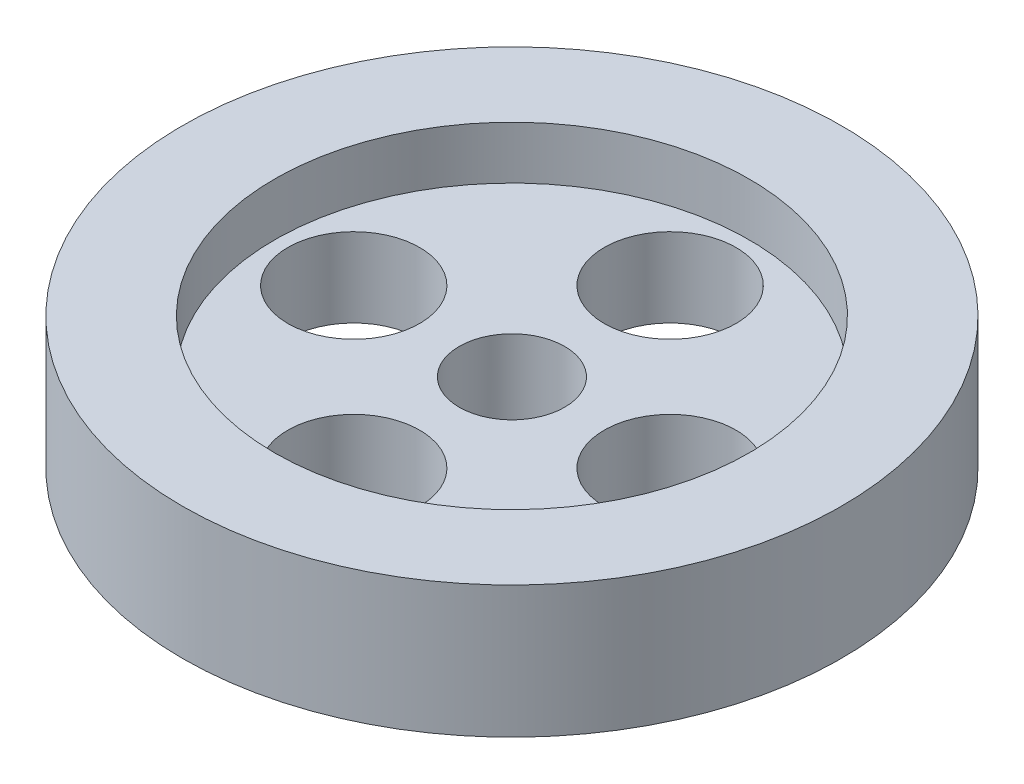
SolidWorks part; units mm, degrees
ref_plane "Front Plane" through (0, 0, 0) normal (0, 0, 1) x (1, 0, 0)
ref_plane "Top Plane" through (0, 0, 0) normal (0, 1, 0) x (1, 0, 0)
ref_plane "Right Plane" through (0, 0, 0) normal (1, 0, 0) x (0, 0, -1)
sketch "Sketch1" plane through (0, 0, 0) normal (0, 1, 0) x (1, 0, 0)
  circle A0 centre (0, 0) radius 25
  circle A1 centre (0, 0) radius 12 construction
  circle A2 centre (0, 0) radius 4
  circle A3 centre (0, 12) radius 5
  circle A4 centre (12, 0) radius 5
  circle A5 centre (0, -12) radius 5
  circle A6 centre (-12, 0) radius 5
  dimension "D1" = 50
  dimension "D2" = 24
  dimension "D3" = 8
  dimension "D4" = 10
  dimension "D5" = 4
extrude "Boss-Extrude1" add sketch "Sketch1" along normal blind 10
sketch "Sketch2" plane through (0, 10, 0) normal (0, 1, 0) x (1, 0, 0)
  circle A0 centre (0, 0) radius 18
  dimension "D1" = 36
extrude "Cut-Extrude1" cut sketch "Sketch2" against normal blind 4
sketch "Sketch3" plane through (0, 0, 0) normal (0, -1, 0) x (1, 0, 0)
  circle A0 centre (0, 0) radius 6
  dimension "D1" = 12
extrude "Boss-Extrude2" add sketch "Sketch3" along normal blind 1
sketch "Sketch4" plane through (0, 0, 0) normal (0, 1, 0) x (1, 0, 0)
  circle A1 centre (0, 0) radius 4
  circle A2 centre (0, 0) radius 4
  dimension "D1" = 0
extrude "Cut-Extrude2" cut sketch "Sketch4" against normal blind 13
